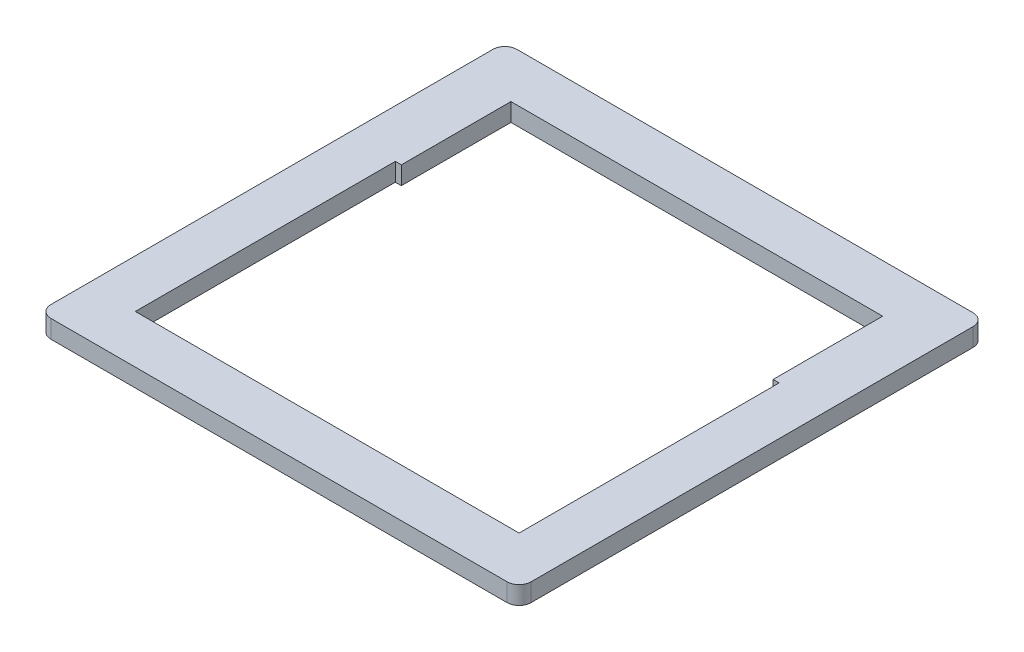
SolidWorks part; units mm, degrees
material "有机玻璃 (TM) GS 丙烯酸铸钣"
ref_plane "前视基准面" through (0, 0, 0) normal (0, 0, 1) x (1, 0, 0)
ref_plane "上视基准面" through (0, 0, 0) normal (0, 1, 0) x (1, 0, 0)
ref_plane "右视基准面" through (0, 0, 0) normal (1, 0, 0) x (0, 0, -1)
sketch "草图1" plane through (0, 0, 0) normal (0, 1, 0) x (1, 0, 0)
  line L0 (-28.1223, 20.6558) -> (-28.1223, 38.8446)
  line L1 (-29.1223, 20.6558) -> (-28.1223, 20.6558)
  line L2 (-29.1223, 20.6558) -> (-29.1223, -22.5027)
  line L3 (-29.1223, -22.5027) -> (34.5798, -22.5027)
  line L4 (34.5798, 20.6558) -> (34.5798, -22.5027)
  line L5 (-35.1223, 46.8446) -> (40.5798, 46.8446)
  line L6 (-37.1223, 44.8446) -> (-37.1223, -28.5027)
  line L7 (-35.1223, -30.5027) -> (40.5798, -30.5027)
  line L8 (42.5798, 44.8446) -> (42.5798, -28.5027)
  line L9 (33.5798, 20.6558) -> (33.5798, 38.8446)
  line L10 (-28.1223, 38.8446) -> (33.5798, 38.8446)
  line L11 (33.5798, 20.6558) -> (34.5798, 20.6558)
  arc A0 (-37.1223, 44.8446) -> (-35.1223, 46.8446) centre (-35.1223, 44.8446) cw
  arc A1 (-37.1223, -28.5027) -> (-35.1223, -30.5027) centre (-35.1223, -28.5027) ccw
  arc A2 (40.5798, -30.5027) -> (42.5798, -28.5027) centre (40.5798, -28.5027) ccw
  arc A3 (42.5798, 44.8446) -> (40.5798, 46.8446) centre (40.5798, 44.8446) ccw
  dimension "D6" = 2
  dimension "D7" = 2
  dimension "D1" = 8
  dimension "D2" = 8
  dimension "D3" = 8
  dimension "D4" = 1
  dimension "D5" = 1
  dimension "D8" = 8
extrude "凸台-拉伸1" add sketch "草图1" along normal blind 3
sketch "草图2" plane through (0, 3, 0) normal (0, 1, 0) x (1, 0, 0)
  circle A0 centre (-32.6106, -21.331) radius 2.8222
